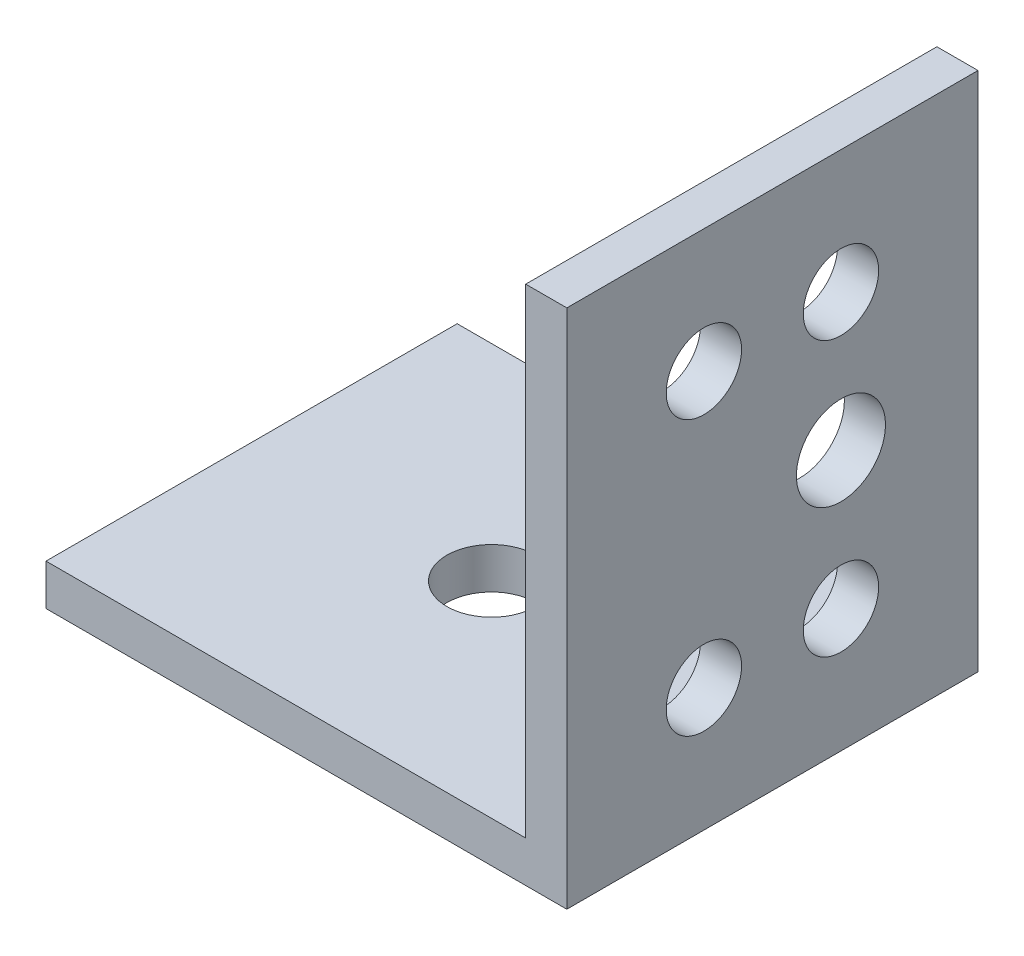
SolidWorks part; units mm, degrees
ref_plane "前视基准面" through (0, 0, 0) normal (0, 0, 1) x (1, 0, 0)
ref_plane "上视基准面" through (0, 0, 0) normal (0, 1, 0) x (1, 0, 0)
ref_plane "右视基准面" through (0, 0, 0) normal (1, 0, 0) x (0, 0, -1)
sketch "草图1" plane through (0, 0, 0) normal (0, 0, 1) x (1, 0, 0)
  line L0 (0, 0) -> (0, 38)
  line L1 (0, 0) -> (-38, 0)
  line L2 (-38, 0) -> (-38, 3)
  line L3 (-38, 3) -> (-3, 3)
  line L4 (-3, 3) -> (-3, 38)
  line L5 (-3, 38) -> (0, 38)
  dimension "D1" = 35
  dimension "D2" = 3
  dimension "D3" = 3
  dimension "D4" = 35
extrude "凸台-拉伸1" add sketch "草图1" along normal blind 30
sketch "草图4" plane through (0, 0, 0) normal (1, 0, 0) x (0, 0, -1)
  line L0 (0, 0) -> (0, 38) construction
  line L2 (-30, 38) -> (0, 38) construction
  circle A0 centre (-10, 29) radius 2.75
  circle A1 centre (-10, 19) radius 3.25
  circle A2 centre (-10, 9) radius 2.75
  circle A3 centre (-20, 29) radius 2.75
  circle A4 centre (-20, 9) radius 2.75
  dimension "D3" = 5.5
  dimension "D4" = 6.5
  dimension "D5" = 5.5
  dimension "D7" = 5.5
  dimension "D9" = 5.5
  dimension "D1" = 10
  dimension "D2" = 10
  dimension "D6" = 10
  dimension "D8" = 20
  dimension "D10" = 10
  dimension "D11" = 19
extrude "切除-拉伸3" cut sketch "草图4" against normal up to next
sketch "草图5" plane through (0, 3, 0) normal (0, 1, 0) x (1, 0, 0)
  line L0 (-38, -30) -> (-38, 0) construction
  line L2 (-3, 0) -> (-38, 0) construction
  circle A0 centre (-20.5, -15) radius 3.25
  dimension "D1" = 6.5
  dimension "D2" = 17.5
  dimension "D3" = 15
extrude "切除-拉伸4" cut sketch "草图5" against normal up to next
